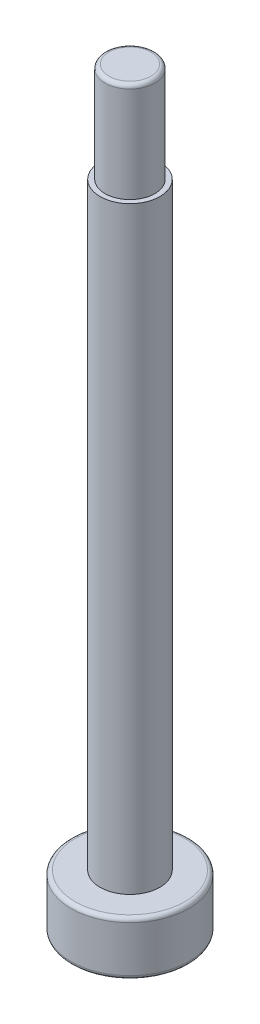
SolidWorks part; units mm, degrees
ref_plane "前视基准面" through (0, 0, 0) normal (0, 0, 1) x (1, 0, 0)
ref_plane "上视基准面" through (0, 0, 0) normal (0, 1, 0) x (1, 0, 0)
ref_plane "右视基准面" through (0, 0, 0) normal (1, 0, 0) x (0, 0, -1)
sketch "草图1" plane through (0, 0, 0) normal (0, 1, 0) x (1, 0, 0)
  circle A0 centre (0, 0) radius 2.95
  dimension "D1" = 5.9
extrude "凸台-拉伸1" add sketch "草图1" along normal blind 2.7
sketch "草图2" plane through (0, 2.7, 0) normal (0, 1, 0) x (1, 0, 0)
  circle A0 centre (0, 0) radius 1.5
  dimension "D1" = 3
extrude "凸台-拉伸2" add sketch "草图2" along normal blind 30
sketch "草图3" plane through (0, 32.7, 0) normal (0, 1, 0) x (1, 0, 0)
  circle A0 centre (0, 0) radius 1.25
  dimension "D1" = 2.5
extrude "凸台-拉伸3" add sketch "草图3" along normal blind 5
sketch "草图4" plane through (0, 0, 0) normal (0, -1, 0) x (1, 0, 0)
  line L1 (2.2473, -0.532) -> (1.5844, 1.6802)
  line L2 (1.5844, 1.6802) -> (-0.6629, 2.2122)
  line L3 (-0.6629, 2.2122) -> (-2.2473, 0.532)
  line L4 (-2.2473, 0.532) -> (-1.5844, -1.6802)
  line L5 (-1.5844, -1.6802) -> (0.6629, -2.2122)
  line L6 (0.6629, -2.2122) -> (2.2473, -0.532)
  circle A0 centre (0, 0) radius 2 construction
  dimension "D1" = 4
extrude "切除-拉伸1" cut sketch "草图4" against normal blind 2
fillet "圆角1" radius 0.2 3 edges at (0, 0, 2.95) (0, 2.7, 2.95) (0, 37.7, 1.25)
